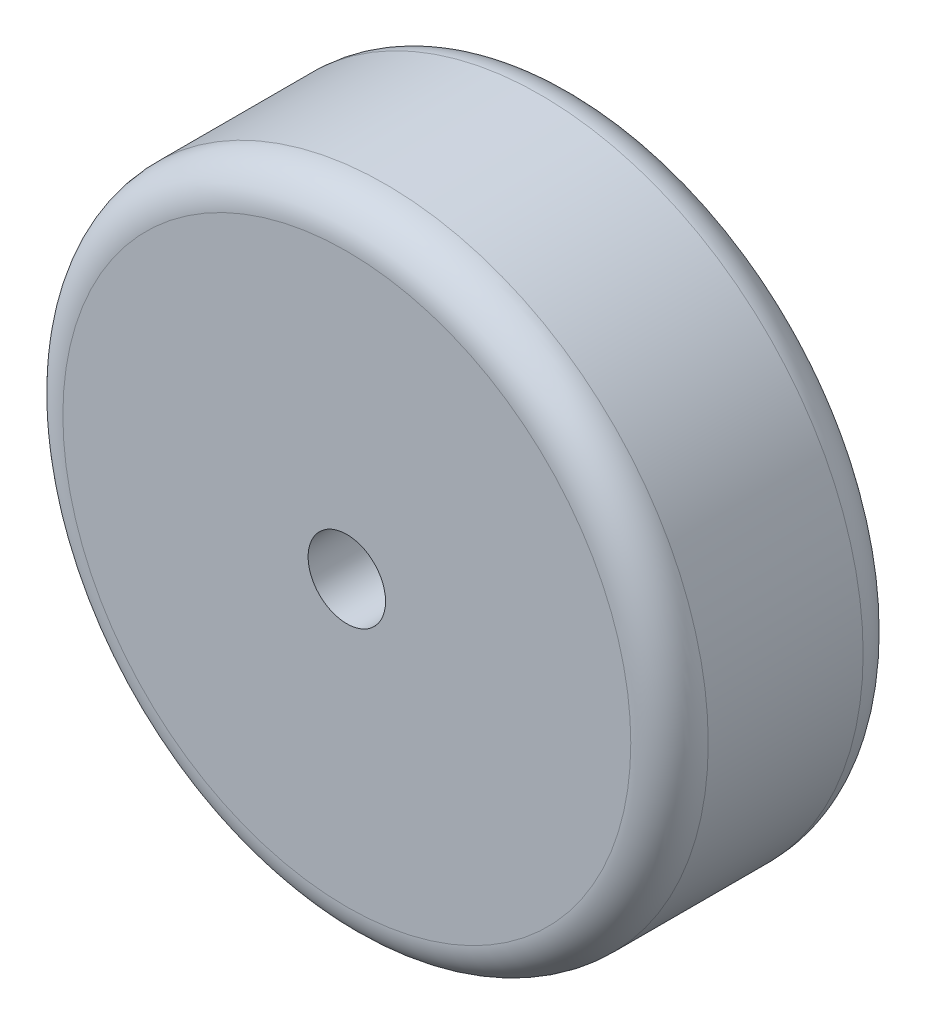
SolidWorks part; units mm, degrees
ref_plane "Front Plane" through (0, 0, 0) normal (0, 0, 1) x (1, 0, 0)
ref_plane "Top Plane" through (0, 0, 0) normal (0, 1, 0) x (1, 0, 0)
ref_plane "Right Plane" through (0, 0, 0) normal (1, 0, 0) x (0, 0, -1)
sketch "Sketch1" plane through (0, 0, 0) normal (0, 0, 1) x (1, 0, 0)
  circle A0 centre (0, 0) radius 25
  circle A1 centre (0, 0) radius 3
  dimension "D1" = 50
  dimension "D2" = 6
extrude "Boss-Extrude1" add sketch "Sketch1" along normal blind 18
fillet "Fillet1" radius 3 2 edges at (25, 0, 18) (25, 0, 0)
